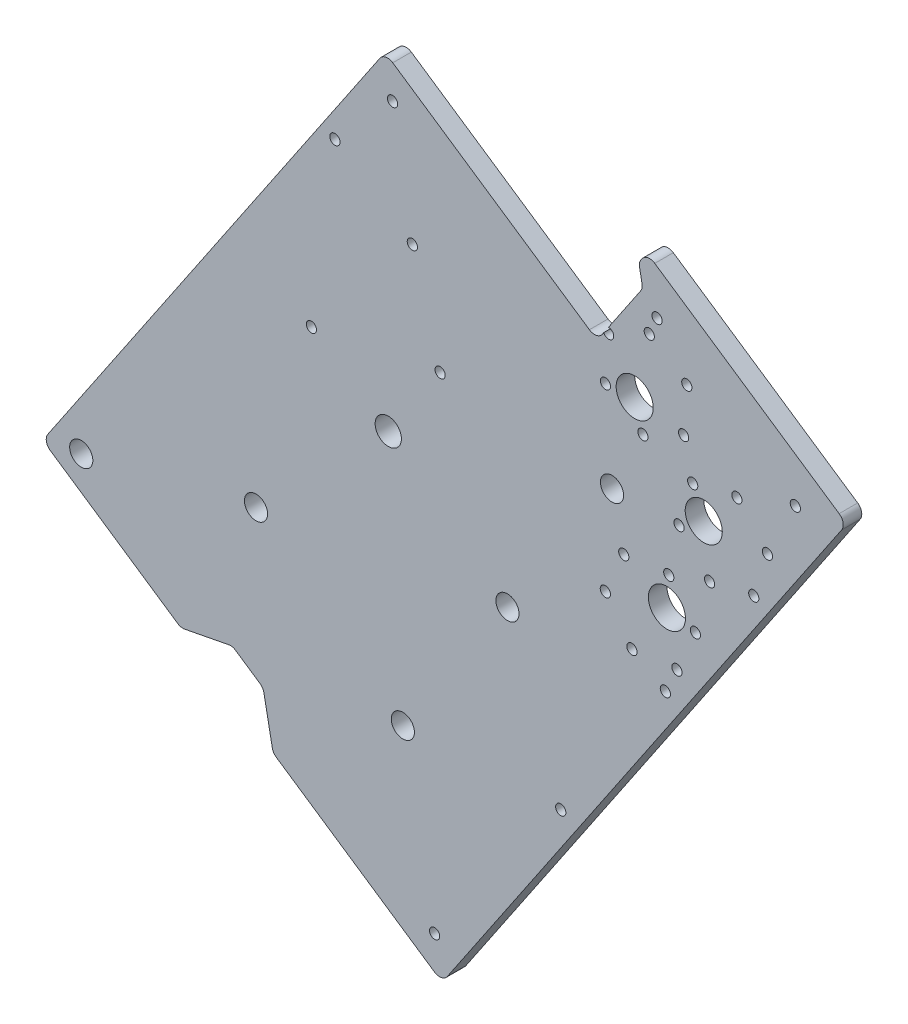
SolidWorks part; units mm, degrees
ref_plane "Front Plane" through (0, 0, 0) normal (0, 0, 1) x (1, 0, 0)
ref_plane "Top Plane" through (0, 0, 0) normal (0, 1, 0) x (1, 0, 0)
ref_plane "Right Plane" through (0, 0, 0) normal (1, 0, 0) x (0, 0, -1)
sketch "Sketch1" plane through (0, 0, 0) normal (0, 0, 1) x (1, 0, 0)
  line L0 (0, 31.75) -> (0, 57.15) construction
  line L1 (31.75, 0) -> (67.31, 0) construction
  line L3 (0, -31.75) -> (0, -97.79) construction
  line L4 (22.4506, -22.4506) -> (58.3717, -58.3717) construction
  line L5 (-22.4506, -22.4506) -> (-72.7401, -72.7401) construction
  line L6 (57.493, 23.8144) -> (29.3332, 12.1502) construction
  line L7 (-40.4112, 40.4112) -> (-22.4506, 22.4506) construction
  line L8 (42.2072, 42.2072) -> (22.4506, 22.4506) construction
  line L9 (71.5729, -29.6465) -> (29.3332, -12.1502) construction
  line L10 (33.5345, -80.9596) -> (12.1502, -29.3332) construction
  line L11 (-37.4226, -90.3462) -> (-12.1502, -29.3332) construction
  circle A0 centre (0, 0) radius 31.75 construction
  circle A3 centre (0, 0) radius 50.8 construction
  dimension "D4" = 63.5
  dimension "D24" = 101.6
  dimension "D2" = 25.4
  dimension "D3" = 35.56
  dimension "D5" = 66.04
  dimension "D6" = 45
  dimension "D7" = 50.8
  dimension "D8" = 71.12
  dimension "D9" = 45
  dimension "D10" = 45
  dimension "D11" = 27.94
  dimension "D12" = 45
  dimension "D13" = 22.5
  dimension "D14" = 22.5
  dimension "D15" = 22.5
  dimension "D16" = 25.4
  dimension "D17" = 45.72
  dimension "D18" = 55.88
  dimension "D19" = 66.04
  dimension "D20" = 22.5
  dimension "D21" = 30.48
sketch "Sketch6" plane through (0, 0, 0) normal (0, 0, 1) x (1, 0, 0)
  line L0 (0, 0) -> (0, 57.15) construction
  line L1 (-68.0069, -76.6709) -> (-109.4868, -48.6565)
  line L2 (-109.4868, -48.6565) -> (-73.9468, 3.9663) construction
  line L3 (-73.9468, 3.9663) -> (-56.6244, -7.7327)
  line L4 (-73.9468, 3.9663) -> (-1.0899, 111.8431)
  line L5 (-1.0899, 111.8431) -> (135.7295, 19.4391)
  line L6 (135.7295, 19.4391) -> (18.4476, -154.2162)
  line L7 (18.4476, -154.2162) -> (-118.3718, -61.8122)
  line L8 (-118.3718, -61.8122) -> (-109.4868, -48.6565)
  arc A0 (0, 57.15) -> (-56.6244, -7.7327) centre (0, 0) ccw
  arc A1 (0, 57.15) -> (70.8293, -29.3385) centre (1.3636, -13.9802) cw
  spline S0 degree 4 poles (72.5802, -14.4204) (72.5732, -14.8939) (72.5509, -15.8408) (72.5026, -17.0238) (72.4142, -18.4418) (72.3202, -19.622) (72.2329, -20.5651) (72.1094, -21.7358) (71.9666, -22.9009) (71.8046, -24.0602) (71.6239, -25.2132) (71.4679, -26.1331) (71.3203, -26.9417) (71.191, -27.6137) (71.0723, -28.2005) (70.9682, -28.6984) (70.8717, -29.1472) (70.8012, -29.4669) (70.7133, -29.8548) (70.619, -30.2629) (70.5011, -30.7621) (70.364, -31.3222) (70.1993, -31.971) (70.0005, -32.7239) (69.7951, -33.4698) (69.582, -34.2143) (69.3614, -34.9567) (69.1333, -35.6968) (68.8388, -36.6189) (68.4706, -37.7207) (68.0195, -38.9988) (67.4748, -40.4488) (66.9013, -41.8877) (66.2993, -43.3149) (65.6691, -44.7298) (65.0111, -46.132) (64.3256, -47.521) (63.613, -48.8963) (62.8736, -50.2574) (62.1078, -51.6038) (61.3159, -52.935) (60.4985, -54.2507) (59.6557, -55.5503) (58.5712, -57.1543) (57.221, -59.0453) (55.576, -61.2004) (53.604, -63.5903) (51.5433, -65.9041) (49.3973, -68.139) (47.1695, -70.2924) (44.8635, -72.3618) (42.4828, -74.3448) (40.0312, -76.2394) (36.8825, -78.4946) (32.9768, -81.016) (28.2508, -83.6809) (21.4155, -86.9191) (14.3083, -89.5267) (6.997, -91.4882) (-0.4519, -92.7974) (-6.6169, -93.4564) (-12.812, -93.702) (-19.0096, -93.5373) (-25.1831, -92.9667) (-31.3064, -91.9964) (-36.5985, -90.8043) (-41.0725, -89.5432) (-44.7523, -88.3359) (-47.6642, -87.2776) (-50.5413, -86.1284) (-53.3811, -84.8896) (-56.1809, -83.563) (-58.5935, -82.3267) (-60.6334, -81.2142) (-62.3138, -80.2525) (-63.6461, -79.4625) (-64.9661, -78.6522) (-66.2736, -77.8217) (-67.4063, -77.0777) (-68.3692, -76.4276) (-69.1659, -75.8779) (-69.7996, -75.4335) (-70.4313, -74.9832) (-71.06, -74.5278) (-71.6725, -74.0775) (-72.2987, -73.6093) (-72.9683, -73.0996) (-73.347, -72.808) (-73.9663, -72.325) (-74.6801, -71.7609) (-75.4046, -71.175) (-76.2838, -70.4507) (-77.1319, -69.735) (-77.9818, -69.0025) (-78.8195, -68.2643) (-79.6511, -67.5155) (-80.4737, -66.7585) (-81.4921, -65.8008) (-82.6974, -64.6343) (-83.8818, -63.4463) (-85.0447, -62.2374) (-85.8084, -61.4205) (-86.1873, -61.0093) (-86.376, -60.8031) knots 0 0 0 0 0 0.008941 0.017882 0.022352 0.026823 0.031293 0.035764 0.044578 0.048985 0.053392 0.057799 0.062207 0.06441 0.066614 0.068817 0.071021 0.072848 0.074676 0.076504 0.078332 0.081987 0.085642 0.089298 0.092953 0.096609 0.100264 0.103919 0.107575 0.114886 0.122197 0.129507 0.136818 0.144129 0.15144 0.158751 0.166062 0.173372 0.180683 0.187994 0.195305 0.202616 0.209927 0.217237 0.231859 0.246481 0.261102 0.275724 0.290346 0.304967 0.319589 0.334211 0.348832 0.363454 0.392697 0.421941 0.451184 0.506141 0.535384 0.564627 0.593871 0.623114 0.652357 0.681601 0.710844 0.740087 0.754709 0.769331 0.783952 0.798574 0.813196 0.827817 0.842439 0.84975 0.857061 0.864371 0.871682 0.878993 0.886304 0.889959 0.893615 0.89727 0.900926 0.904581 0.908237 0.911892 0.915547 0.918186 0.920826 0.926104 0.931382 0.936661 0.941939 0.947217 0.952495 0.957774 0.963052 0.96833 0.978887 0.989443 0.994722 1 1 1 1 1 construction
  spline S1 degree 4 poles (70.8293, -29.3385) (70.8117, -29.4183) (70.776, -29.5781) (70.7133, -29.8548) (70.619, -30.2629) (70.5011, -30.7621) (70.364, -31.3222) (70.1993, -31.971) (70.0005, -32.7239) (69.7951, -33.4698) (69.582, -34.2143) (69.3614, -34.9567) (69.1333, -35.6968) (68.8388, -36.6189) (68.4706, -37.7207) (68.0195, -38.9988) (67.4748, -40.4488) (66.9013, -41.8877) (66.2993, -43.3149) (65.6691, -44.7298) (65.0111, -46.132) (64.3256, -47.521) (63.613, -48.8963) (62.8736, -50.2574) (62.1078, -51.6038) (61.3159, -52.935) (60.4985, -54.2507) (59.6557, -55.5503) (58.5712, -57.1543) (57.221, -59.0453) (55.576, -61.2004) (53.604, -63.5903) (51.5433, -65.9041) (49.3973, -68.139) (47.1695, -70.2924) (44.8635, -72.3618) (42.4828, -74.3448) (40.0312, -76.2394) (36.8825, -78.4946) (32.9768, -81.016) (28.2508, -83.6809) (21.4155, -86.9191) (14.3083, -89.5267) (6.997, -91.4882) (-0.4519, -92.7974) (-6.6169, -93.4564) (-12.812, -93.702) (-19.0096, -93.5373) (-25.1831, -92.9667) (-31.3064, -91.9964) (-36.5985, -90.8043) (-41.0725, -89.5432) (-44.7523, -88.3359) (-47.6642, -87.2776) (-50.5413, -86.1284) (-53.3811, -84.8896) (-56.1809, -83.563) (-58.5935, -82.3267) (-60.6334, -81.2142) (-62.3138, -80.2525) (-63.6461, -79.4625) (-64.9661, -78.6522) (-66.2224, -77.8543) (-67.143, -77.2506) (-67.7363, -76.8537) (-68.0069, -76.6709) knots 0.071021 0.071021 0.071021 0.071021 0.071021 0.072848 0.074676 0.076504 0.078332 0.081987 0.085642 0.089298 0.092953 0.096609 0.100264 0.103919 0.107575 0.114886 0.122197 0.129507 0.136818 0.144129 0.15144 0.158751 0.166062 0.173372 0.180683 0.187994 0.195305 0.202616 0.209927 0.217237 0.231859 0.246481 0.261102 0.275724 0.290346 0.304967 0.319589 0.334211 0.348832 0.363454 0.392697 0.421941 0.451184 0.506141 0.535384 0.564627 0.593871 0.623114 0.652357 0.681601 0.710844 0.740087 0.754709 0.769331 0.783952 0.798574 0.813196 0.827817 0.842439 0.84975 0.857061 0.864371 0.871682 0.878993 0.885158 0.885158 0.885158 0.885158 0.885158
  dimension "D1" = 57.15
  dimension "D2" = 101.6
  dimension "D3" = 63.5
  dimension "D4" = 63.5
  dimension "D5" = 15.875
  dimension "D6" = 101.6
  dimension "D7" = 209.55
extrude "Boss-Extrude2" add sketch "Sketch6" along normal blind 6.35
sketch "Sketch8" plane through (0, 0, 6.35) normal (0, 0, 1) x (1, 0, 0)
  line L0 (-71.0112, -93.7982) -> (-53.3787, -90.3816)
  line L1 (-118.3718, -61.8122) -> (18.4476, -154.2162) construction
  line L2 (-53.3787, -90.3816) -> (-42.8541, -97.4896)
  line L3 (-42.8541, -97.4896) -> (-39.4375, -115.1222)
  line L4 (-39.4375, -115.1222) -> (-71.0112, -93.7982)
  line L5 (18.4476, -154.2162) -> (135.7295, 19.4391) construction
  dimension "D1" = 82.55
  dimension "D2" = 12.7
  dimension "D3" = 12.7
  dimension "D4" = 45
  dimension "D5" = 45
extrude "Cut-Extrude1" cut sketch "Sketch8" against normal through all
sketch "Sketch9" plane through (0, 0, 6.35) normal (0, 0, 1) x (1, 0, 0)
  line L0 (-1.0899, 111.8431) -> (-109.4868, -48.6565)
  line L1 (-1.0899, 111.8431) -> (135.7295, 19.4391)
  line L2 (-109.4868, -48.6565) -> (27.3325, -141.0605)
  line L3 (135.7295, 19.4391) -> (27.3325, -141.0605)
  line L4 (18.4476, -154.2162) -> (135.7295, 19.4391) construction
extrude "Boss-Extrude3" add sketch "Sketch9" against normal through all
sketch "Sketch10" plane through (0, 0, 6.35) normal (0, 0, 1) x (1, 0, 0)
  line L0 (76.6361, 21.2777) -> (4.9965, -84.7966) construction
  line L2 (-39.4375, -115.1222) -> (18.4476, -154.2162) construction
  line L3 (0, 0) -> (-45.2952, -45.2145) construction
  line L4 (-45.2952, -45.2145) -> (4.9965, -84.7966) construction
  line L5 (18.4476, -154.2162) -> (135.7295, 19.4391) construction
  circle A0 centre (4.9965, -84.7966) radius 3.9688
  circle A1 centre (40.8163, -31.7595) radius 3.9687
  circle A2 centre (76.6361, 21.2777) radius 3.9687
  circle A3 centre (-45.2952, -45.2145) radius 3.9687
  dimension "D1" = 7.9375
  dimension "D2" = 50
  dimension "D3" = 50
  dimension "D4" = 128
  dimension "D5" = 64
extrude "Cut-Extrude2" cut sketch "Sketch10" against normal through all
sketch "Sketch11" plane through (0, 0, 6.35) normal (0, 0, 1) x (1, 0, 0)
  circle A0 centre (0, 0) radius 4.5
  dimension "D1" = 9
extrude "Cut-Extrude4" cut sketch "Sketch11" against normal through all contours A0
sketch "Sketch12" plane through (0, 0, 6.35) normal (0, 0, 1) x (1, 0, 0)
  line L0 (135.7295, 19.4391) -> (67.3198, 65.6411)
  line L1 (135.7295, 19.4391) -> (157.0534, 51.0128)
  line L2 (67.3198, 65.6411) -> (88.6438, 97.2148)
  line L3 (157.0534, 51.0128) -> (88.6438, 97.2148)
  line L4 (135.7295, 19.4391) -> (-1.0899, 111.8431) construction
  dimension "D1" = 82.55
  dimension "D2" = 38.1
extrude "Boss-Extrude4" add sketch "Sketch12" against normal through all
sketch "Sketch13" plane through (0, 0, 6.35) normal (0, 0, 1) x (1, 0, 0)
  line L0 (40.8163, -31.7595) -> (76.6361, 21.2777) construction
  line L1 (18.4476, -154.2162) -> (157.0534, 51.0128) construction
  line L2 (58.7262, -5.2409) -> (94.8992, -29.6711) construction
  circle A0 centre (94.8992, -29.6711) radius 1.75
  dimension "D1" = 3.5
  dimension "D2" = 6.35
extrude "Cut-Extrude5" cut sketch "Sketch13" against normal through all
pattern_linear "LPattern1" count 2 spacing 64 along (-0.5597, -0.8287, 0) of "Cut-Extrude5"
sketch "Sketch15" plane through (0, 0, 6.35) normal (0, 0, 1) x (1, 0, 0)
  line L0 (-118.3718, -61.8122) -> (-71.0112, -93.7982) construction
  line L1 (-39.4375, -115.1222) -> (18.4476, -154.2162) construction
  line L2 (18.4476, -154.2162) -> (157.0534, 51.0128) construction
  line L3 (-1.0899, 111.8431) -> (-118.3718, -61.8122) construction
  line L4 (67.3198, 65.6411) -> (-1.0899, 111.8431) construction
  circle A0 centre (-105.1473, -59.2498) radius 1.75
  circle A1 centre (15.8851, -140.9917) radius 1.75
  circle A2 centre (59.0794, -82.7083) radius 1.75 construction
  circle A3 centre (1.4726, 98.6186) radius 1.75
  dimension "D1" = 9.525
  dimension "D2" = 9.525
  dimension "D3" = 9.525
  dimension "D4" = 9.525
  dimension "D5" = 9.525
  dimension "D6" = 9.525
extrude "Cut-Extrude7" cut sketch "Sketch15" against normal through all
sketch "Sketch16" plane through (0, 0, 6.35) normal (0, 0, 1) x (1, 0, 0)
  line L0 (157.0534, 51.0128) -> (88.6438, 97.2148) construction
  line L1 (88.6438, 97.2148) -> (67.3198, 65.6411) construction
  line L2 (18.4476, -154.2162) -> (157.0534, 51.0128) construction
  circle A0 centre (92.0604, 79.5822) radius 1.75
  circle A1 centre (139.4209, 47.5962) radius 1.75
  circle A2 centre (94.8992, -29.6711) radius 1.75 construction
  dimension "D1" = 12.7
  dimension "D2" = 12.7
  dimension "D3" = 12.7
  dimension "D4" = 12.7
extrude "Cut-Extrude8" cut sketch "Sketch16" against normal through all
sketch "Sketch17" plane through (0, 0, 6.35) normal (0, 0, 1) x (1, 0, 0)
  line L0 (0, 0) -> (-26.3114, 17.77) construction
  line L1 (0, 0) -> (17.77, 26.3114) construction
  line L2 (18.4476, -154.2162) -> (157.0534, 51.0128) construction
  circle A0 centre (-26.3114, 17.77) radius 1.75
  circle A1 centre (17.77, 26.3114) radius 1.75
  circle A2 centre (94.8992, -29.6711) radius 1.75 construction
  dimension "D1" = 31.75
extrude "Cut-Extrude9" cut sketch "Sketch17" against normal through all
sketch "Sketch18" plane through (0, 0, 6.35) normal (0, 0, 1) x (1, 0, 0)
  line L0 (76.6361, 21.2777) -> (108.0518, 27.3649) construction
  line L1 (157.0534, 51.0128) -> (88.6438, 97.2148) construction
  line L2 (76.6361, 21.2777) -> (84.396, 52.3226) construction
  line L3 (76.6361, 21.2777) -> (95.4299, -4.622) construction
  line L4 (95.4299, -4.622) -> (89.7643, -8.7331) construction
  line L5 (108.0518, 27.3649) -> (114.7254, 25.2525) construction
  line L6 (84.396, 52.3226) -> (88.3138, 58.1235) construction
  line L7 (88.6438, 97.2148) -> (67.3198, 65.6411) construction
  line L10 (89.7643, -8.7331) -> (114.7254, 25.2525) construction
  line L11 (114.7254, 25.2525) -> (88.3138, 58.1235) construction
  line L13 (87.2234, 42.6619) -> (101.1588, 49.4484) construction
  line L14 (101.1588, 49.4484) -> (102.2492, 64.91) construction
  line L15 (102.2492, 64.91) -> (89.4042, 73.5851) construction
  line L16 (89.4042, 73.5851) -> (75.4689, 66.7986) construction
  line L17 (75.4689, 66.7986) -> (74.3785, 51.337) construction
  line L18 (74.3785, 51.337) -> (87.2234, 42.6619) construction
  line L19 (99.5891, 21.9147) -> (110.0478, 10.4751) construction
  line L20 (110.0478, 10.4751) -> (125.1842, 13.8128) construction
  line L21 (125.1842, 13.8128) -> (129.8618, 28.5902) construction
  line L22 (129.8618, 28.5902) -> (119.4031, 40.0298) construction
  line L23 (119.4031, 40.0298) -> (104.2667, 36.6921) construction
  line L24 (104.2667, 36.6921) -> (99.5891, 21.9147) construction
  line L25 (105.1804, -7.1221) -> (96.0772, 5.4231) construction
  line L26 (96.0772, 5.4231) -> (80.6611, 3.812) construction
  line L27 (80.6611, 3.812) -> (74.3483, -10.3442) construction
  line L28 (74.3483, -10.3442) -> (83.4515, -22.8894) construction
  line L29 (83.4515, -22.8894) -> (98.8676, -21.2783) construction
  line L30 (98.8676, -21.2783) -> (105.1804, -7.1221) construction
  circle A0 centre (114.7254, 25.2525) radius 18.5 construction
  circle A1 centre (88.3138, 58.1235) radius 18.5 construction
  circle A2 centre (89.7643, -8.7331) radius 18.5 construction
  circle A3 centre (88.3138, 58.1235) radius 13.4234 construction
  circle A4 centre (114.7254, 25.2525) radius 13.4234 construction
  circle A5 centre (89.7643, -8.7331) radius 13.4234 construction
  circle A6 centre (75.4689, 66.7986) radius 1.75
  circle A7 centre (74.3785, 51.337) radius 1.75
  circle A8 centre (87.2234, 42.6619) radius 1.75
  circle A9 centre (101.1588, 49.4484) radius 1.75
  circle A10 centre (102.2492, 64.91) radius 1.75
  circle A11 centre (89.4042, 73.5851) radius 1.75
  circle A12 centre (99.5891, 21.9147) radius 1.75
  circle A13 centre (104.2667, 36.6921) radius 1.75
  circle A14 centre (119.4031, 40.0298) radius 1.75
  circle A15 centre (129.8618, 28.5902) radius 1.75
  circle A16 centre (125.1842, 13.8128) radius 1.75
  circle A17 centre (110.0478, 10.4751) radius 1.75
  circle A18 centre (105.1804, -7.1221) radius 1.75
  circle A19 centre (96.0772, 5.4231) radius 1.75
  circle A20 centre (80.6611, 3.812) radius 1.75
  circle A21 centre (74.3483, -10.3442) radius 1.75
  circle A22 centre (83.4515, -22.8894) radius 1.75
  circle A23 centre (98.8676, -21.2783) radius 1.75
  circle A24 centre (84.396, 52.3226) radius 6.35
  circle A25 centre (108.0518, 27.3649) radius 6.35
  circle A26 centre (95.4299, -4.622) radius 6.35
  dimension "D6" = 37
  dimension "D8" = 3.5
  dimension "D9" = 12.7
  dimension "D1" = 45
  dimension "D2" = 65
  dimension "D3" = 65
  dimension "D4" = 32
  dimension "D5" = 7
  dimension "D7" = 31
extrude "Cut-Extrude10" cut sketch "Sketch18" against normal through all
sketch "Sketch19" plane through (0, 0, 6.35) normal (0, 0, 1) x (1, 0, 0)
  line L0 (88.6438, 97.2148) -> (67.3198, 65.6411) construction
  line L1 (67.3198, 65.6411) -> (-1.0899, 111.8431) construction
  line L2 (18.4476, -154.2162) -> (-118.3718, -61.8122) construction
  line L3 (-65.6802, -85.9048) -> (35.6087, 64.0702) construction
  line L4 (-73.9468, 3.9663) -> (-1.0899, 111.8431) construction
  circle A0 centre (35.6087, 64.0702) radius 3.9687 construction
  circle A1 centre (-65.6802, -85.9048) radius 3.9687
  dimension "D1" = 7.9375
  dimension "D2" = 25.4
  dimension "D3" = 19.05
  dimension "D4" = 9.525
extrude "Cut-Extrude11" cut sketch "Sketch19" against normal through all
sketch "Sketch20" plane through (0, 0, 6.35) normal (0, 0, 1) x (1, 0, 0)
  circle A0 centre (-105.1473, -59.2498) radius 3.9688
  dimension "D1" = 7.9375
extrude "Cut-Extrude12" cut sketch "Sketch20" against normal through all
sketch "Sketch21" plane through (0, 0, 6.35) normal (0, 0, 1) x (1, 0, 0)
  circle A0 centre (-65.6802, -85.9048) radius 5.6777
extrude "Boss-Extrude5" add sketch "Sketch21" against normal through all
sketch "Sketch22" plane through (0, 0, 6.35) normal (0, 0, 1) x (1, 0, 0)
  line L0 (85.8006, 93.0049) -> (87.1672, 85.9519)
  line L1 (88.6438, 97.2148) -> (67.3198, 65.6411) construction
  line L2 (87.1672, 85.9519) -> (71.5296, 62.7979)
  line L3 (71.5296, 62.7979) -> (67.3198, 65.6411)
  line L4 (67.3198, 65.6411) -> (85.8006, 93.0049)
  line L5 (67.3198, 65.6411) -> (-1.0899, 111.8431) construction
  dimension "D1" = 5.08
  dimension "D3" = 45
  dimension "D4" = 5.08
extrude "Cut-Extrude13" cut sketch "Sketch22" against normal through all
sketch "Sketch23" plane through (0, 0, 0) normal (0, 0, -1) x (-1, 0, 0)
  line L0 (22.4138, 80.2694) -> (-8.2483, 59.561) construction
  line L1 (1.0899, 111.8431) -> (118.3718, -61.8122) construction
  line L2 (-71.5296, 62.7979) -> (1.0899, 111.8431) construction
  circle A0 centre (-8.2483, 59.561) radius 1.75
  circle A1 centre (18.2703, 77.4709) radius 1.75
  dimension "D3" = 3.5
  dimension "D1" = 32
  dimension "D2" = 5
  dimension "D4" = 38.1
extrude "Cut-Extrude14" cut sketch "Sketch23" against normal through all
fillet "Fillet1" radius 3.175 12 edges at (-71.0112, -93.7982, 3.175) (-53.3787, -90.3816, 3.175) (-42.8541, -97.4896, 3.175) (-39.4375, -115.1222, 3.175) (-118.3718, -61.8122, 3.175) (18.4476, -154.2162, 3.175) (157.0534, 51.0128, 3.175) (-1.0899, 111.8431, 3.175) (87.1672, 85.9519, 3.175) (71.5296, 62.7979, 3.175) (85.8006, 93.0049, 3.175) (88.6438, 97.2148, 3.175)
